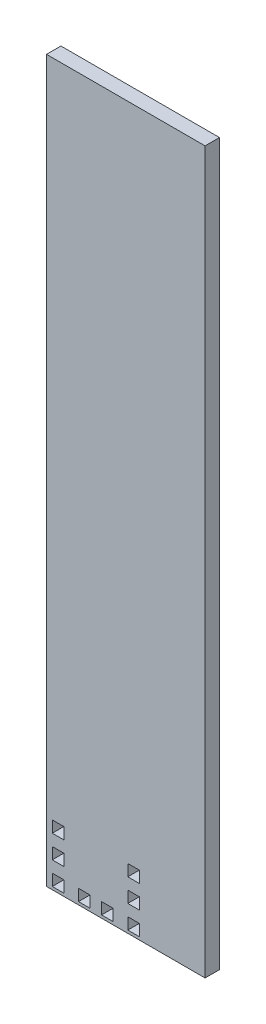
SolidWorks part; units mm, degrees
ref_plane "Plan de face" through (0, 0, 0) normal (0, 0, 1) x (1, 0, 0)
ref_plane "Plan de dessus" through (0, 0, 0) normal (0, 1, 0) x (1, 0, 0)
ref_plane "Plan de droite" through (0, 0, 0) normal (1, 0, 0) x (0, 0, -1)
sketch "Esquisse1" plane through (0, 0, 0) normal (0, 0, 1) x (1, 0, 0)
  line L1 (0, 0) -> (55, 0)
  line L2 (0, 0) -> (0, 250)
  line L3 (0, 250) -> (55, 250)
  line L4 (55, 0) -> (55, 250)
  line L17 (32.2, 21) -> (28.2, 21)
  line L18 (32.2, 21) -> (32.2, 17)
  line L19 (32.2, 17) -> (28.2, 17)
  line L20 (28.2, 21) -> (28.2, 17)
  line L21 (32.2, 13) -> (28.2, 13)
  line L22 (32.2, 13) -> (32.2, 9)
  line L23 (32.2, 9) -> (28.2, 9)
  line L24 (28.2, 13) -> (28.2, 9)
  line L25 (32.2, 5) -> (28.2, 5)
  line L26 (32.2, 5) -> (32.2, 1)
  line L27 (32.2, 1) -> (28.2, 1)
  line L28 (28.2, 5) -> (28.2, 1)
  line L29 (23.1, 1) -> (19.1, 1)
  line L30 (23.1, 1) -> (23.1, 5)
  line L31 (23.1, 5) -> (19.1, 5)
  line L32 (19.1, 1) -> (19.1, 5)
  line L33 (15.1, 1) -> (11.1, 1)
  line L34 (15.1, 1) -> (15.1, 5)
  line L35 (15.1, 5) -> (11.1, 5)
  line L36 (11.1, 1) -> (11.1, 5)
  line L37 (6, 1) -> (2, 1)
  line L38 (6, 1) -> (6, 5)
  line L39 (6, 5) -> (2, 5)
  line L40 (2, 1) -> (2, 5)
  line L41 (2, 9) -> (6, 9)
  line L42 (2, 9) -> (2, 13)
  line L43 (2, 13) -> (6, 13)
  line L44 (6, 9) -> (6, 13)
  line L45 (2, 17) -> (6, 17)
  line L46 (2, 17) -> (2, 21)
  line L47 (2, 21) -> (6, 21)
  line L48 (6, 17) -> (6, 21)
  dimension "D1" = 250
  dimension "D2" = 55
  dimension "D4" = 22.2
  dimension "D6" = 16
  dimension "D15" = 4
  dimension "D16" = 4
  dimension "D17" = 4
  dimension "D18" = 4
  dimension "D19" = 4
  dimension "D20" = 4
  dimension "D21" = 4
  dimension "D22" = 4
  dimension "D23" = 4
  dimension "D24" = 4
  dimension "D25" = 4
  dimension "D26" = 4
  dimension "D27" = 4
  dimension "D28" = 4
  dimension "D29" = 4
  dimension "D30" = 4
  dimension "D31" = 4
  dimension "D32" = 5.1
  dimension "D33" = 4
  dimension "D34" = 5.1
  dimension "D35" = 4
extrude "Boss.-Extru.1" add sketch "Esquisse1" along normal blind 5
